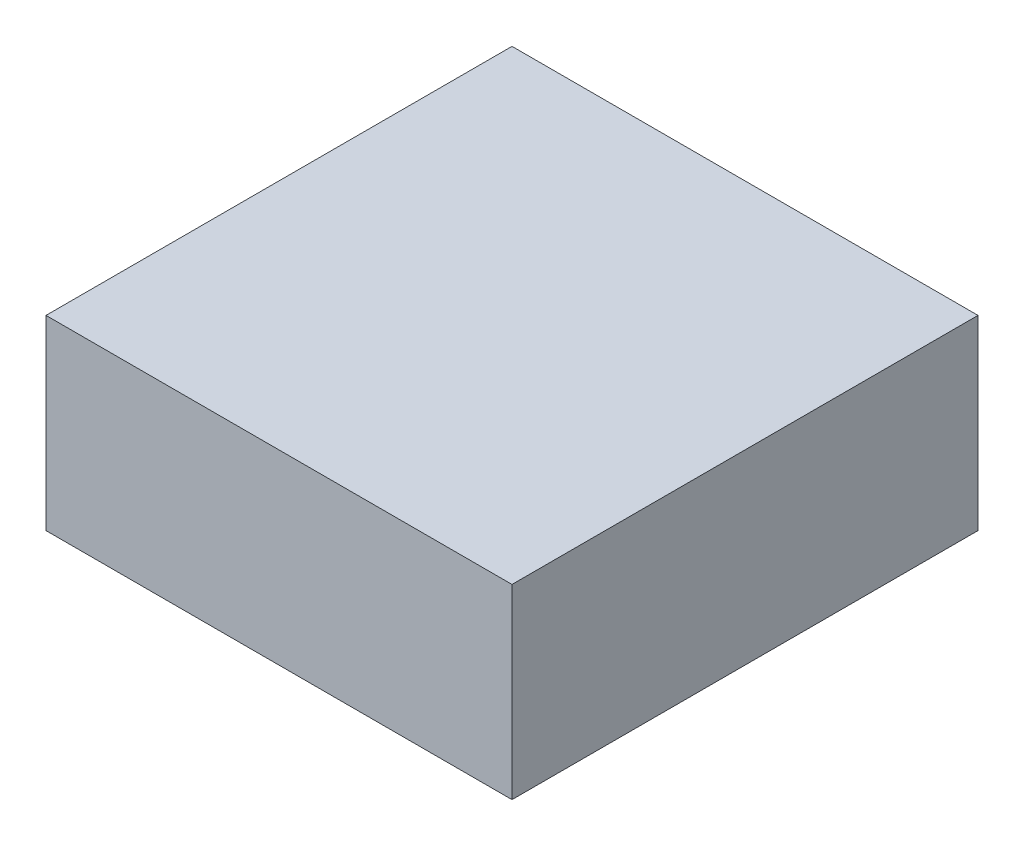
SolidWorks part; units mm, degrees
ref_plane "Front Plane" through (0, 0, 0) normal (0, 0, 1) x (1, 0, 0)
ref_plane "Top Plane" through (0, 0, 0) normal (0, 1, 0) x (1, 0, 0)
ref_plane "Right Plane" through (0, 0, 0) normal (1, 0, 0) x (0, 0, -1)
sketch "Sketch1" plane through (0, 0, 0) normal (0, 1, 0) x (1, 0, 0)
  line L1 (0, 0) -> (15.875, 0)
  line L2 (0, 0) -> (0, 15.875)
  line L3 (0, 15.875) -> (15.875, 15.875)
  line L4 (15.875, 0) -> (15.875, 15.875)
  dimension "D1" = 15.875
extrude "Boss-Extrude1" add sketch "Sketch1" along normal blind 6.35
